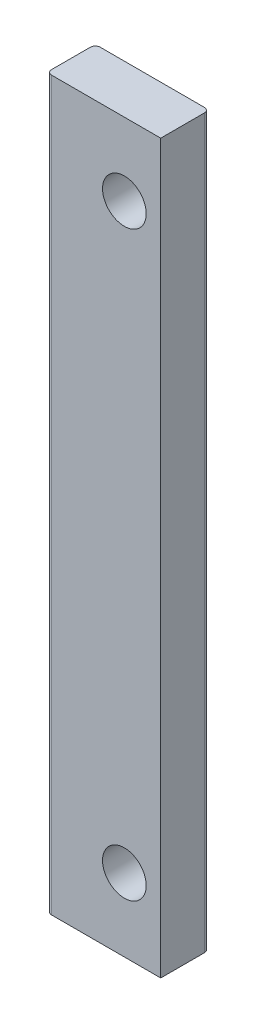
SolidWorks part; units mm, degrees
ref_plane "Front Plane" through (0, 0, 0) normal (0, 0, 1) x (1, 0, 0)
ref_plane "Top Plane" through (0, 0, 0) normal (0, 1, 0) x (1, 0, 0)
ref_plane "Right Plane" through (0, 0, 0) normal (1, 0, 0) x (0, 0, -1)
sketch "Sketch1" plane through (0, 0, 0) normal (0, 1, 0) x (1, 0, 0)
  line L1 (-10.75, -5) -> (11.75, -5)
  line L2 (-11.75, -4) -> (-11.75, 4)
  line L3 (-10.75, 5) -> (10.75, 5)
  line L4 (11.75, -5) -> (11.75, 4)
  line L5 (-11.75, -5) -> (11.75, 5) construction
  line L6 (-11.75, 5) -> (11.75, -5) construction
  arc A0 (10.75, 5) -> (11.75, 4) centre (10.75, 4) cw
  arc A1 (-10.75, -5) -> (-11.75, -4) centre (-10.75, -4) cw
  arc A2 (-11.75, 4) -> (-10.75, 5) centre (-10.75, 4) cw
  point P0 (0, 0)
  dimension "D3" = 1
  dimension "D1" = 10
  dimension "D2" = 23.5
extrude "Boss-Extrude1" add sketch "Sketch1" along normal blind 150
sketch "Sketch2" plane through (0, 0, -5) normal (0, 0, -1) x (-1, 0, 0)
  line L0 (-4.25, 0) -> (-4.25, 150) construction
  line L1 (-10.75, 0) -> (10.75, 0) construction
  line L2 (-10.75, 150) -> (10.75, 150) construction
  line L3 (-11.75, 75) -> (10.75, 75) construction
  line L4 (-11.75, 150) -> (-11.75, 0) construction
  line L5 (10.75, 150) -> (10.75, 0) construction
  point P12 (-4.25, 135)
  point P13 (-4.25, 15)
  dimension "D1" = 7.5
  dimension "D2" = 60
  dimension "D3" = 60
hole_wizard "M8 Clearance Hole1" positions "Sketch4" profile "Sketch5" hole size "M8" standard "ANSI Metric" end condition through all
sketch "Sketch4" plane through (0, 0, -5) normal (0, 0, -1) x (-1, 0, 0)
  point P0 (-4.25, 135)
  point P3 (-4.25, 15)
sketch "Sketch5" plane through (4.25, 135, -5) normal (1, 0, 0) x (0, 1, 0)
  line L0 (0, 0) -> (0, 10)
  line L1 (0, 10) -> (4.5, 10)
  line L2 (4.5, 10) -> (4.5, 0)
  line L5 (4.5, 0) -> (0, 0)
  line L11 (0, -6.35) -> (0, 107.95) construction
  dimension "Thru Hole Dia." = 9
  dimension "Thru Hole Depth" = 10
